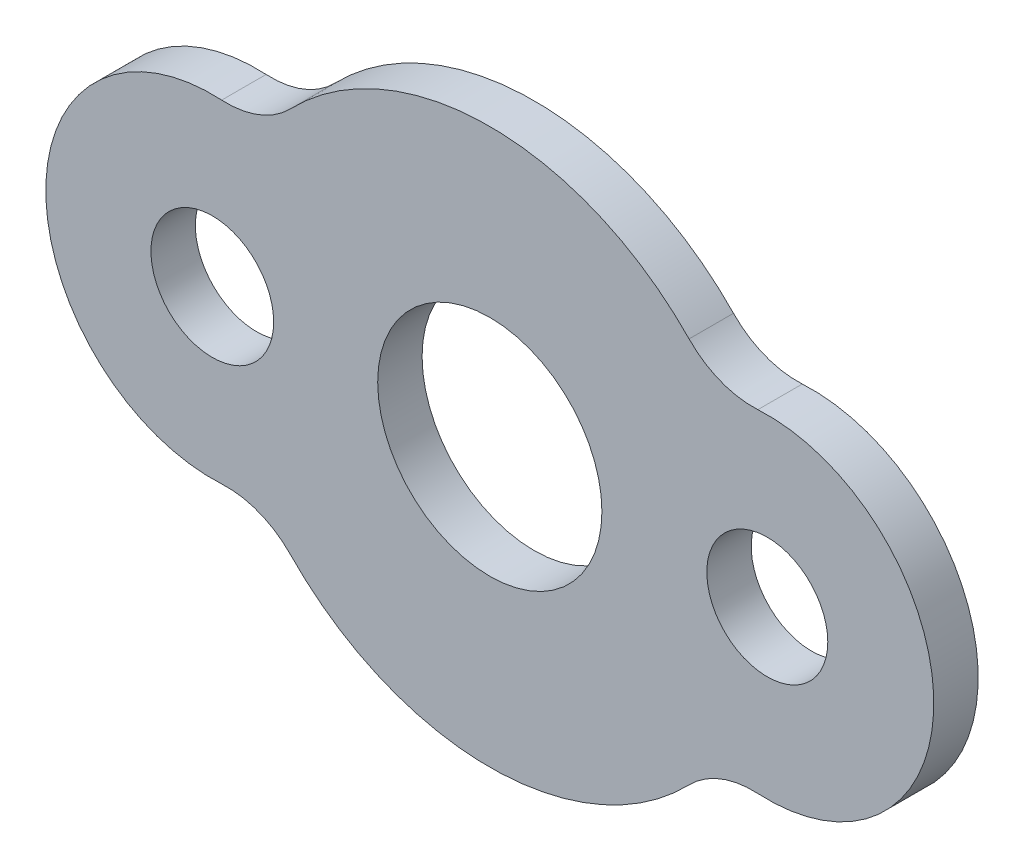
SolidWorks part; units mm, degrees
ref_plane "Płaszczyzna przednia" through (0, 0, 0) normal (0, 0, 1) x (1, 0, 0)
ref_plane "Płaszczyzna górna" through (0, 0, 0) normal (0, 1, 0) x (1, 0, 0)
ref_plane "Płaszczyzna prawa" through (0, 0, 0) normal (1, 0, 0) x (0, 0, -1)
sketch "Szkic1" plane through (0, 0, 0) normal (0, 0, 1) x (1, 0, 0)
  circle A0 centre (0, 0) radius 50.5
  arc A1 (-89.7727, -86.9819) -> (89.7727, -86.9819) centre (0, 0) ccw
  arc A2 (50.201, 5.4872) -> (50.201, -5.4872) centre (125, 0) ccw
  arc A3 (-120.7609, 74.8801) -> (-120.7609, -74.8801) centre (-125, 0) ccw
  arc A4 (-50.201, -5.4872) -> (-50.201, 5.4872) centre (-125, 0) ccw
  arc A5 (89.7727, 86.9819) -> (-89.7727, 86.9819) centre (0, 0) ccw
  arc A6 (120.7609, -74.8801) -> (120.7609, 74.8801) centre (125, 0) ccw
  arc A7 (120.7609, 74.8801) -> (89.7727, 86.9819) centre (118.5, 114.8162) cw
  arc A8 (89.7727, -86.9819) -> (120.7609, -74.8801) centre (118.5, -114.8162) cw
  arc A9 (-120.7609, -74.8801) -> (-89.7727, -86.9819) centre (-118.5, -114.8162) cw
  arc A10 (-120.7609, 74.8801) -> (-89.7727, 86.9819) centre (-118.5, 114.8162) ccw
  circle A11 centre (-125, 0) radius 27.6362
  circle A12 centre (125, 0) radius 27.2458
  point P15 (102.5, 71.5454)
  point P18 (102.5, -71.5454)
  dimension "D1" = 101
  dimension "D2" = 250
  dimension "D3" = 55.2723
  dimension "D4" = 54.4916
  dimension "D5" = 40
extrude "Dodanie-wyciągnięcie1" add sketch "Szkic1" along normal blind 20 contours A10 A3 A9 A1 A8 A6 A7 A5 A12 A11 A0
